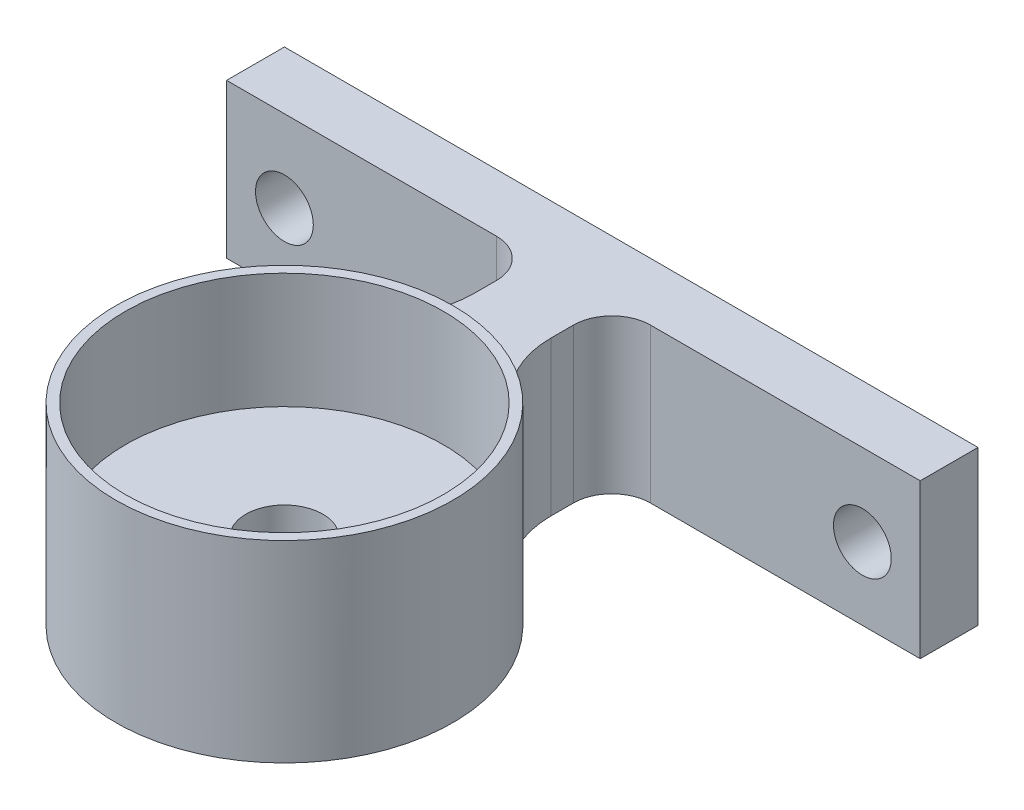
SolidWorks part; units mm, degrees
ref_plane "前视基准面" through (0, 0, 0) normal (0, 0, 1) x (1, 0, 0)
ref_plane "上视基准面" through (0, 0, 0) normal (0, 1, 0) x (1, 0, 0)
ref_plane "右视基准面" through (0, 0, 0) normal (1, 0, 0) x (0, 0, -1)
sketch "草图1" plane through (0, 0, 0) normal (0, 1, 0) x (1, 0, 0)
  circle A0 centre (0, 0) radius 8.25
  circle A1 centre (0, 0) radius 8.75
  dimension "D1" = 16.5
  dimension "D2" = 17.5
extrude "凸台-拉伸2" add sketch "草图1" along normal blind 10
sketch "草图2" plane through (0, 0, 0) normal (0, 1, 0) x (1, 0, 0)
  circle A0 centre (0, 0) radius 8.25
  circle A1 centre (0, 0) radius 2
  dimension "D1" = 4
extrude "凸台-拉伸3" add sketch "草图2" along normal blind 4
sketch "草图3" plane through (0, 0, 0) normal (0, 1, 0) x (1, 0, 0)
  line L0 (-2, 8.5184) -> (2, 8.5184)
  line L1 (-15, 18) -> (-15, 15)
  line L2 (2, 18) -> (15, 18)
  line L3 (-2, 8.5184) -> (-2, 15)
  line L4 (2, 8.5184) -> (2, 15)
  line L5 (-15, 18) -> (-2, 18)
  line L6 (-15, 15) -> (-2, 15)
  line L7 (15, 15) -> (15, 18)
  line L8 (2, 15) -> (15, 15)
  line L9 (2, 18) -> (-2, 18)
  circle A2 centre (0, 0) radius 8.75 construction
  dimension "D1" = 13
  dimension "D2" = 13
  dimension "D3" = 3
  dimension "D4" = 3
extrude "凸台-拉伸4" add sketch "草图3" along normal blind 8
sketch "草图5" plane through (15, 0, 0) normal (1, 0, 0) x (0, 0, -1)
  line L0 (15, 8) -> (18, 8)
  line L1 (15, 8) -> (15, 0)
  line L2 (18, 8) -> (18, 0)
  line L3 (15, 0) -> (18, 0)
  dimension "D1" = 8
extrude "凸台-拉伸5" add sketch "草图5" along normal blind 3
sketch "草图6" plane through (-15, 0, 0) normal (-1, 0, 0) x (0, 0, 1)
  line L0 (-18, 8) -> (-15, 8)
  line L1 (-18, 8) -> (-18, 0)
  line L2 (-15, 8) -> (-15, 0)
  line L3 (-18, 0) -> (-15, 0)
  dimension "D1" = 8
extrude "凸台-拉伸6" add sketch "草图6" along normal blind 3
sketch "草图7" plane through (0, 0, -18) normal (0, 0, -1) x (-1, 0, 0)
  circle A0 centre (-15, 3.754) radius 1.5
  dimension "D2" = 3
extrude "切除-拉伸1" cut sketch "草图7" against normal blind 3
mirror "镜向1" about plane through (0, 0, 0) normal (1, 0, 0) of "切除-拉伸1"
fillet "圆角1" radius 5 2 edges at (2, 4, -8.5184) (-2, 4, -8.5184)
fillet "圆角3" radius 2 2 edges at (-2, 4, -15) (2, 4, -15)
ref_plane "基准面1" through (0, 0, 10) normal (0, 0, 1) x (1, 0, 0)
sketch "草图8" plane through (0, 0, 0) normal (0, 1, 0) x (1, 0, 0)
  circle A0 centre (27.185, 0) radius 8.75
  circle A1 centre (27.185, 0) radius 8.25
  dimension "D1" = 17.5
  dimension "D2" = 16.5
extrude "凸台-拉伸7" add sketch "草图8" along normal blind 8 separate body
sketch "草图9" plane through (0, 0, 0) normal (0, -1, 0) x (1, 0, 0)
  circle A0 centre (27.185, 0) radius 8.25
  circle A1 centre (27.185, 0) radius 6
  dimension "D1" = 12
extrude "凸台-拉伸8" add sketch "草图9" against normal blind 2
sketch "草图10" plane through (0, 0, 0) normal (0, 1, 0) x (1, 0, 0)
  line L1 (27.185, -18) -> (45.185, -18)
  line L2 (27.185, -18) -> (9.185, -18)
  line L3 (9.185, -18) -> (9.185, -14.6639)
  line L4 (9.185, -14.6639) -> (25.185, -14.6639)
  line L5 (45.185, -18) -> (45.185, -14.6639)
  line L6 (45.185, -14.6639) -> (29.185, -14.6639)
  line L7 (25.185, -14.6639) -> (25.185, -8.5184)
  line L8 (25.185, -8.5184) -> (29.185, -8.5184)
  line L9 (29.185, -8.5184) -> (29.185, -14.6639)
  circle A0 centre (27.185, 0) radius 8.75 construction
  dimension "D2" = 18
  dimension "D3" = 18
  dimension "D4" = 16
  dimension "D5" = 16
extrude "凸台-拉伸9" add sketch "草图10" along normal blind 8
sketch "草图11" plane through (0, 0, 18) normal (0, 0, 1) x (1, 0, 0)
  circle A0 centre (12.185, 4) radius 1.5
  circle A1 centre (42.185, 4) radius 1.5
  dimension "D3" = 3
  dimension "D4" = 3
  dimension "D2" = 30
extrude "切除-拉伸2" cut sketch "草图11" against normal blind 8
sketch "草图12" plane through (0, 0, 18) normal (0, 0, 1) x (1, 0, 0)
  line L0 (10.685, 4) -> (10.685, 5)
  line L1 (13.685, 4) -> (13.685, 5)
  line L2 (10.685, 4) -> (10.685, 3)
  line L3 (13.685, 4) -> (13.685, 3)
  circle A0 centre (12.185, 4) radius 1.5 construction
  arc A1 (13.685, 5) -> (10.685, 5) centre (12.185, 5) ccw
  arc A2 (10.685, 3) -> (13.685, 3) centre (12.185, 3) ccw
  dimension "D1" = 1
  dimension "D2" = 1
  dimension "D3" = 1
  dimension "D4" = 1
extrude "切除-拉伸3" cut sketch "草图12" against normal blind 8
sketch "草图13" plane through (0, 0, 18) normal (0, 0, 1) x (1, 0, 0)
  line L0 (40.685, 4) -> (40.685, 5)
  line L2 (43.685, 5) -> (43.685, 4)
  line L3 (43.685, 4) -> (43.685, 3)
  line L5 (40.685, 3) -> (40.685, 4)
  circle A0 centre (42.185, 4) radius 1.5 construction
  arc A1 (43.685, 5) -> (40.685, 5) centre (42.185, 5) ccw
  arc A2 (40.685, 3) -> (43.685, 3) centre (42.185, 3) ccw
  dimension "D1" = 1
  dimension "D2" = 1
  dimension "D3" = 1
extrude "切除-拉伸4" cut sketch "草图13" against normal blind 8
sketch "草图14" plane through (0, 0, 0) normal (0, 1, 0) x (1, 0, 0)
  circle A0 centre (-35.0916, 0) radius 8.75
  circle A1 centre (-35.0916, 0) radius 8.25
  dimension "D1" = 17.5
  dimension "D2" = 16.5
extrude "凸台-拉伸10" add sketch "草图14" along normal blind 8 separate body
sketch "草图15" plane through (0, 0, 0) normal (0, 1, 0) x (1, 0, 0)
  line L0 (-37.0916, -15) -> (-37.0916, -8.5184)
  line L2 (-17.0916, -18) -> (-53.0916, -18)
  line L3 (-53.0916, -18) -> (-53.0916, -15)
  line L4 (-53.0916, -15) -> (-37.0916, -15)
  line L5 (-37.0916, -8.5184) -> (-33.0916, -8.5184)
  line L6 (-33.0916, -15) -> (-17.0916, -15)
  line L7 (-17.0916, -15) -> (-17.0916, -18)
  line L8 (-33.0916, -8.5184) -> (-33.0916, -15)
  circle A0 centre (-35.0916, 0) radius 8.75 construction
  dimension "D4" = 3
  dimension "D5" = 16
  dimension "D6" = 16
extrude "凸台-拉伸11" add sketch "草图15" along normal blind 8
sketch "草图16" plane through (0, 0, 18) normal (0, 0, 1) x (1, 0, 0)
  circle A0 centre (-50.0916, 4) radius 1.5
  circle A1 centre (-20.0916, 4) radius 1.5
  dimension "D3" = 3
  dimension "D4" = 3
extrude "切除-拉伸5" cut sketch "草图16" against normal blind 8
sketch "草图17" plane through (0, 0, 0) normal (0, 1, 0) x (1, 0, 0)
  line L0 (-33.9377, 15.4057) -> (-2.7222, -15.8098)
  line L1 (-2.7222, -15.8098) -> (14.647, -5.0781)
  line L2 (14.647, -5.0781) -> (14.647, 8.9156)
  line L3 (14.647, 8.9156) -> (41.968, 12.7607)
  line L4 (41.968, 12.7607) -> (60.5316, -22.7612)
  line L5 (60.5316, -22.7612) -> (-4.0343, -33.8915)
  line L6 (-4.0343, -33.8915) -> (-68.1837, -30.7671)
  line L7 (-68.1837, -30.7671) -> (-78.8046, -10.444)
  line L8 (-78.8046, -10.444) -> (-56.2875, 12.0731)
  line L9 (-56.2875, 12.0731) -> (-33.9377, 15.4057)
extrude "切除-拉伸6" cut sketch "草图17" along normal blind 10
